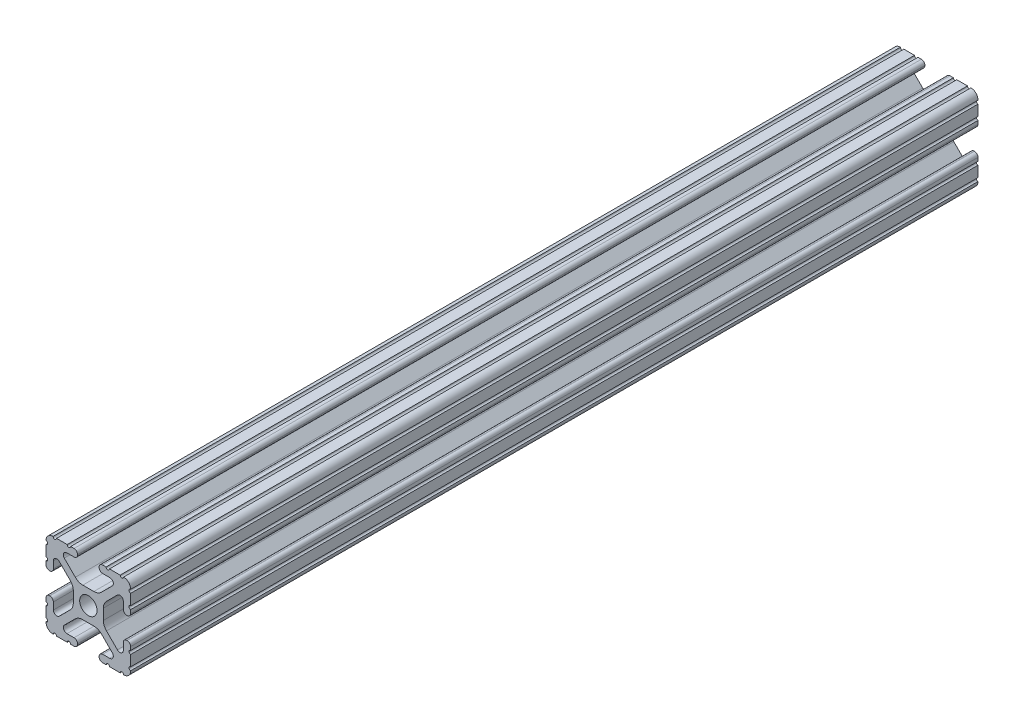
SolidWorks part; units mm, degrees
material "1060 Alloy"
ref_plane "Front Plane" through (0, 0, 0) normal (0, 0, 1) x (1, 0, 0)
ref_plane "Top Plane" through (0, 0, 0) normal (0, 1, 0) x (1, 0, 0)
ref_plane "Right Plane" through (0, 0, 0) normal (1, 0, 0) x (0, 0, -1)
sketch "Sketch1" plane through (0, 0, 0) normal (0, 0, 1) x (1, 0, 0)
  line L88 (-7.1797, -8.6452) -> (-3.9523, -5.4237)
  line L89 (-1.7093, -4.4958) -> (1.7093, -4.4958)
  line L90 (3.9523, -5.4237) -> (7.1797, -8.6452)
  line L91 (6.4164, -10.4902) -> (4.2875, -10.4902)
  line L92 (3.2385, -11.5392) -> (3.2385, -11.651)
  line L93 (4.2875, -12.7) -> (5.3171, -12.7)
  line L94 (6.3331, -12.7) -> (9.5504, -12.7)
  line L95 (12.7, -9.5504) -> (12.7, -6.3331)
  line L96 (12.7, -5.3171) -> (12.7, -4.2875)
  line L97 (11.651, -3.2385) -> (11.5392, -3.2385)
  line L98 (10.4902, -4.2875) -> (10.4902, -6.4021)
  line L99 (8.7371, -7.1294) -> (5.441, -3.8408)
  line L100 (4.5085, -1.5932) -> (4.5085, 1.5932)
  line L101 (5.441, 3.8408) -> (8.7371, 7.1294)
  line L102 (10.4902, 6.4021) -> (10.4902, 4.2875)
  line L103 (11.5392, 3.2385) -> (11.651, 3.2385)
  line L104 (12.7, 4.2875) -> (12.7, 5.3171)
  line L105 (12.7, 6.3331) -> (12.7, 9.5504)
  line L106 (9.5504, 12.7) -> (6.3331, 12.7)
  line L107 (5.3171, 12.7) -> (4.2875, 12.7)
  line L108 (3.2385, 11.651) -> (3.2385, 11.5392)
  line L109 (4.2875, 10.4902) -> (6.4768, 10.4902)
  line L110 (7.207, 8.7244) -> (3.8983, 5.4232)
  line L111 (1.6558, 4.4958) -> (-1.6558, 4.4958)
  line L112 (-3.8983, 5.4232) -> (-7.207, 8.7244)
  line L113 (-6.4768, 10.4902) -> (-4.2875, 10.4902)
  line L114 (-3.2385, 11.5392) -> (-3.2385, 11.651)
  line L115 (-4.2875, 12.7) -> (-5.3171, 12.7)
  line L116 (-6.3331, 12.7) -> (-9.5504, 12.7)
  line L117 (-12.7, 9.5504) -> (-12.7, 6.3331)
  line L118 (-12.7, 5.3171) -> (-12.7, 4.2875)
  line L119 (-11.651, 3.2385) -> (-11.5392, 3.2385)
  line L120 (-10.4902, 4.2875) -> (-10.4902, 6.4021)
  line L121 (-8.7371, 7.1294) -> (-5.441, 3.8408)
  line L122 (-4.5085, 1.5932) -> (-4.5085, -1.5932)
  line L123 (-5.441, -3.8408) -> (-8.7371, -7.1294)
  line L124 (-10.4902, -6.4021) -> (-10.4902, -4.2875)
  line L125 (-11.5392, -3.2385) -> (-11.651, -3.2385)
  line L126 (-12.7, -4.2875) -> (-12.7, -5.3171)
  line L127 (-12.7, -6.3331) -> (-12.7, -9.5504)
  line L128 (-9.5504, -12.7) -> (-6.3331, -12.7)
  line L129 (-5.3171, -12.7) -> (-4.2875, -12.7)
  line L130 (-3.2385, -11.651) -> (-3.2385, -11.5392)
  line L131 (-4.2875, -10.4902) -> (-6.4164, -10.4902)
  circle A1 centre (0, 0) radius 2.6035
  arc A104 (-7.1797, -8.6452) -> (-6.4164, -10.4902) centre (-6.4164, -9.4098) ccw
  arc A105 (-1.7093, -4.4958) -> (-3.9523, -5.4237) centre (-1.7093, -7.6708) ccw
  arc A106 (3.9523, -5.4237) -> (1.7093, -4.4958) centre (1.7093, -7.6708) ccw
  arc A107 (6.4164, -10.4902) -> (7.1797, -8.6452) centre (6.4164, -9.4098) ccw
  arc A108 (4.2875, -10.4902) -> (3.2385, -11.5392) centre (4.2875, -11.5392) ccw
  arc A109 (3.2385, -11.651) -> (4.2875, -12.7) centre (4.2875, -11.651) ccw
  arc A110 (6.3331, -12.7) -> (5.3171, -12.7) centre (5.8251, -12.7) ccw
  arc A111 (10.5664, -12.6998) -> (9.5504, -12.7) centre (10.0584, -12.7) ccw
  arc A112 (10.5664, -12.6998) -> (12.6998, -10.5664) centre (10.5918, -10.5918) ccw
  arc A113 (12.7, -9.5504) -> (12.6998, -10.5664) centre (12.7, -10.0584) ccw
  arc A114 (12.7, -5.3171) -> (12.7, -6.3331) centre (12.7, -5.8251) ccw
  arc A115 (12.7, -4.2875) -> (11.651, -3.2385) centre (11.651, -4.2875) ccw
  arc A116 (11.5392, -3.2385) -> (10.4902, -4.2875) centre (11.5392, -4.2875) ccw
  arc A117 (8.7371, -7.1294) -> (10.4902, -6.4021) centre (9.4628, -6.4021) ccw
  arc A118 (4.5085, -1.5932) -> (5.441, -3.8408) centre (7.6835, -1.5932) ccw
  arc A119 (5.441, 3.8408) -> (4.5085, 1.5932) centre (7.6835, 1.5932) ccw
  arc A120 (10.4902, 6.4021) -> (8.7371, 7.1294) centre (9.4628, 6.4021) ccw
  arc A121 (10.4902, 4.2875) -> (11.5392, 3.2385) centre (11.5392, 4.2875) ccw
  arc A122 (11.651, 3.2385) -> (12.7, 4.2875) centre (11.651, 4.2875) ccw
  arc A123 (12.7, 6.3331) -> (12.7, 5.3171) centre (12.7, 5.8251) ccw
  arc A124 (12.6998, 10.5664) -> (12.7, 9.5504) centre (12.7, 10.0584) ccw
  arc A125 (12.6998, 10.5664) -> (10.5664, 12.6998) centre (10.5918, 10.5918) ccw
  arc A126 (9.5504, 12.7) -> (10.5664, 12.6998) centre (10.0584, 12.7) ccw
  arc A127 (5.3171, 12.7) -> (6.3331, 12.7) centre (5.8251, 12.7) ccw
  arc A128 (4.2875, 12.7) -> (3.2385, 11.651) centre (4.2875, 11.651) ccw
  arc A129 (3.2385, 11.5392) -> (4.2875, 10.4902) centre (4.2875, 11.5392) ccw
  arc A130 (7.207, 8.7244) -> (6.4768, 10.4902) centre (6.4768, 9.4563) ccw
  arc A131 (1.6558, 4.4958) -> (3.8983, 5.4232) centre (1.6558, 7.6708) ccw
  arc A132 (-3.8983, 5.4232) -> (-1.6558, 4.4958) centre (-1.6558, 7.6708) ccw
  arc A133 (-6.4768, 10.4902) -> (-7.207, 8.7244) centre (-6.4768, 9.4563) ccw
  arc A134 (-4.2875, 10.4902) -> (-3.2385, 11.5392) centre (-4.2875, 11.5392) ccw
  arc A135 (-3.2385, 11.651) -> (-4.2875, 12.7) centre (-4.2875, 11.651) ccw
  arc A136 (-6.3331, 12.7) -> (-5.3171, 12.7) centre (-5.8251, 12.7) ccw
  arc A137 (-10.5664, 12.6998) -> (-9.5504, 12.7) centre (-10.0584, 12.7) ccw
  arc A138 (-10.5664, 12.6998) -> (-12.6998, 10.5664) centre (-10.5918, 10.5918) ccw
  arc A139 (-12.7, 9.5504) -> (-12.6998, 10.5664) centre (-12.7, 10.0584) ccw
  arc A140 (-12.7, 5.3171) -> (-12.7, 6.3331) centre (-12.7, 5.8251) ccw
  arc A141 (-12.7, 4.2875) -> (-11.651, 3.2385) centre (-11.651, 4.2875) ccw
  arc A142 (-11.5392, 3.2385) -> (-10.4902, 4.2875) centre (-11.5392, 4.2875) ccw
  arc A143 (-8.7371, 7.1294) -> (-10.4902, 6.4021) centre (-9.4628, 6.4021) ccw
  arc A144 (-4.5085, 1.5932) -> (-5.441, 3.8408) centre (-7.6835, 1.5932) ccw
  arc A145 (-5.441, -3.8408) -> (-4.5085, -1.5932) centre (-7.6835, -1.5932) ccw
  arc A146 (-10.4902, -6.4021) -> (-8.7371, -7.1294) centre (-9.4628, -6.4021) ccw
  arc A147 (-10.4902, -4.2875) -> (-11.5392, -3.2385) centre (-11.5392, -4.2875) ccw
  arc A148 (-11.651, -3.2385) -> (-12.7, -4.2875) centre (-11.651, -4.2875) ccw
  arc A149 (-12.7, -6.3331) -> (-12.7, -5.3171) centre (-12.7, -5.8251) ccw
  arc A150 (-12.6998, -10.5664) -> (-12.7, -9.5504) centre (-12.7, -10.0584) ccw
  arc A151 (-12.6998, -10.5664) -> (-10.5664, -12.6998) centre (-10.5918, -10.5918) ccw
  arc A152 (-9.5504, -12.7) -> (-10.5664, -12.6998) centre (-10.0584, -12.7) ccw
  arc A153 (-5.3171, -12.7) -> (-6.3331, -12.7) centre (-5.8251, -12.7) ccw
  arc A154 (-4.2875, -12.7) -> (-3.2385, -11.651) centre (-4.2875, -11.651) ccw
  arc A155 (-3.2385, -11.5392) -> (-4.2875, -10.4902) centre (-4.2875, -11.5392) ccw
extrude "Boss-Extrude1" add sketch "Sketch1" along normal blind 254.2
